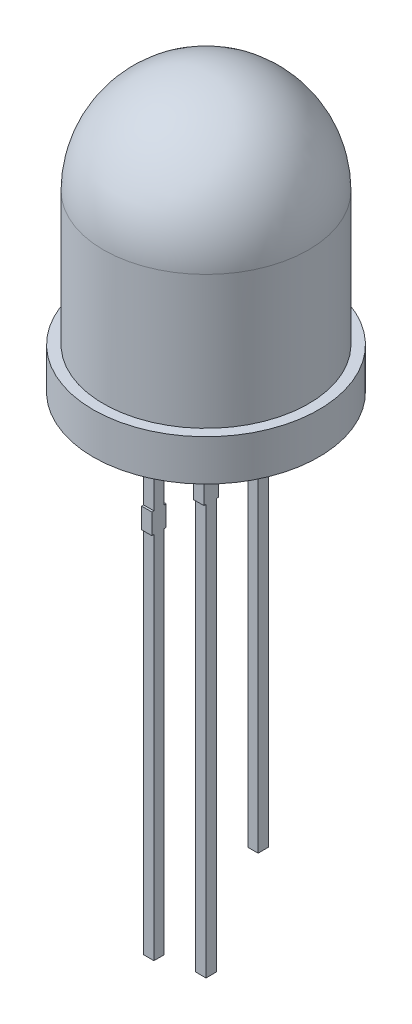
SolidWorks part; units mm, degrees
other "DetailItem2"
ref_plane "Front Plane" through (0, 0, 0) normal (0, 0, 1) x (1, 0, 0)
ref_plane "Top Plane" through (0, 0, 0) normal (0, 1, 0) x (1, 0, 0)
ref_plane "Right Plane" through (0, 0, 0) normal (1, 0, 0) x (0, 0, -1)
sketch "Sketch1" plane through (0, 0, 0) normal (0, 0, 1) x (1, 0, 0)
  line L0 (0, 0) -> (0, 11.5)
  line L1 (5, 6.5) -> (5, 0)
  line L2 (5, 0) -> (0, 0)
  arc A0 (0, 11.5) -> (5, 6.5) centre (0, 6.5) cw
  dimension "D1" = 5
  dimension "D2" = 11.5
revolve "Revolve1" add sketch "Sketch1" angle 360 about L0
ref_plane "Plane1" through (0, -2, 0) normal (0, -1, 0) x (1, 0, 0)
sketch "Sketch2" plane through (0, -2, 0) normal (0, -1, 0) x (1, 0, 0)
  arc A0 (-2.2913, 5) -> (2.2913, 5) centre (0, 0) ccw
  circle A2 centre (0, 0) radius 5.5
  dimension "D1" = 11
  dimension "D2" = 11
extrude "Extrude1" add sketch "Sketch2" against normal up to surface (2 mm away) up to face at (0, 0, -5)
sketch "Sketch3" plane through (0, 0, 0) normal (1, 0, 0) x (0, 0, -1)
  line L0 (-1.79, -2) -> (-1.79, -3)
  line L1 (-5.5, -2) -> (5.5, -2) construction
  line L2 (-1.79, -3) -> (-2.79, -3)
  line L3 (-2.79, -3) -> (-2.79, -24.5)
  line L4 (-2.79, -24.5) -> (-2.29, -24.5)
  line L5 (-2.29, -24.5) -> (-2.29, -3.5)
  line L6 (-2.29, -3.5) -> (-1.29, -3.5)
  line L7 (-1.29, -3.5) -> (-1.29, -2)
  line L8 (-1.29, -2) -> (-1.79, -2)
  line L9 (0.25, -2) -> (0.25, -26.5)
  line L10 (0.25, -26.5) -> (-0.25, -26.5)
  line L11 (-0.25, -26.5) -> (-0.25, -2)
  line L12 (-0.25, -2) -> (0.25, -2)
  line L13 (1.9924, -2) -> (2.79, -3.5)
  line L14 (2.79, -3.5) -> (2.79, -22.5)
  line L15 (2.79, -22.5) -> (2.29, -22.5)
  line L16 (2.29, -22.5) -> (2.29, -3.5)
  line L17 (2.29, -3.5) -> (1.4924, -2)
  line L18 (1.4924, -2) -> (1.9924, -2)
  line L19 (0, 0) -> (0, -7.669) construction
  line L20 (0, -2) -> (0, -3.213) construction
  line L21 (-2.54, -24.5) -> (-2.54, -4.1217) construction
  line L22 (0, -26.5) -> (0, -9.9541) construction
  line L23 (2.54, -22.5) -> (2.54, -5.8969) construction
  line L24 (1.7424, -2) -> (1.7424, -3.8177) construction
  line L25 (-1.54, -2) -> (-1.54, -3.0197) construction
  line L26 (2.54, -5.5) -> (2.54, -6.5) construction
  line L27 (2.89, -5.5) -> (2.19, -5.5)
  line L28 (2.89, -5.5) -> (2.89, -6.5)
  line L29 (2.89, -6.5) -> (2.19, -6.5)
  line L30 (2.19, -5.5) -> (2.19, -6.5)
  line L31 (0, 11.5) -> (0, 3.8149) construction
  line L32 (2.19, -6) -> (-3.6111, -6) construction
  line L33 (0, -5.5) -> (0, -6.5) construction
  line L34 (-2.19, -5.5) -> (-2.89, -5.5)
  line L35 (-2.19, -5.5) -> (-2.19, -6.5)
  line L36 (-2.19, -6.5) -> (-2.89, -6.5)
  line L37 (-2.89, -5.5) -> (-2.89, -6.5)
  line L38 (0.35, -5.5) -> (-0.35, -5.5)
  line L39 (0.35, -5.5) -> (0.35, -6.5)
  line L40 (0.35, -6.5) -> (-0.35, -6.5)
  line L41 (-0.35, -5.5) -> (-0.35, -6.5)
  line L42 (-2.54, -5.5) -> (-2.54, -6.5) construction
  line L43 (0.35, -6) -> (-0.35, -6) construction
  line L44 (-2.19, -6) -> (-2.89, -6) construction
  arc A0 (5, 6.5) -> (-5, 6.5) centre (0, 6.5) ccw construction
  dimension "D1" = 0.5
  dimension "D2" = 0.5
  dimension "D3" = 15
  dimension "D4" = 1
  dimension "D5" = 0.5
  dimension "D6" = 62
  dimension "D7" = 2.54
  dimension "D8" = 2.54
  dimension "D9" = 0.5
  dimension "D10" = 24.5
  dimension "D11" = 2
  dimension "D12" = 4
  dimension "D13" = 0.7
  dimension "D14" = 1
  dimension "D15" = 17
  dimension "D16" = 0.7
  dimension "D17" = 0.7
extrude "Extrude2" add sketch "Sketch3" along normal mid plane 0.5 contours L29 L16 L15 L14 | L16 L27 L14 L13 L18 L17 | L16 L29 L14 L27 | L30 L29 L16 L27 | L14 L29 L28 L27 | L9 L10 L11 L12 | L39 L40 L41 L38 | L35 L36 L37 L34 | L5 L6 L7 L8 L0 L2 L3 L4
sketch "Sketch4" plane through (0, -2, 0) normal (0, -1, 0) x (1, 0, 0)
  line L0 (-3.4439, 4.2883) -> (-3.4439, -4.2883) construction
  circle A0 centre (0, 0) radius 5.5 construction
  text T0 "www.SunLED.com" font "Verdana" height 0.1
extrude "Cut-Extrude1" cut sketch "Sketch4" against normal blind 0.01
